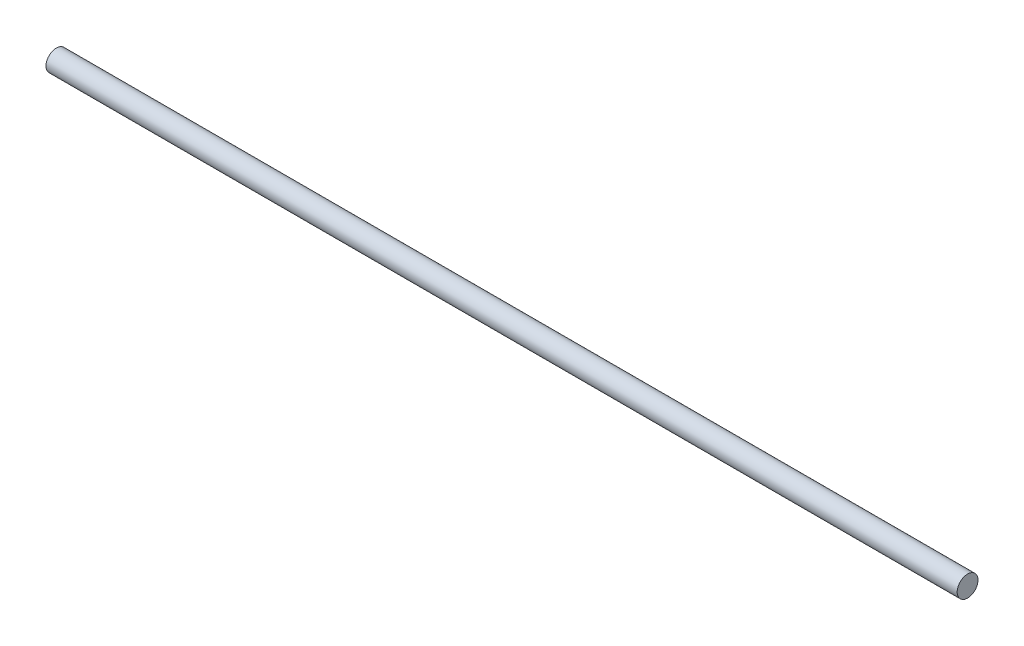
SolidWorks part; units mm, degrees
ref_plane "Front Plane" through (0, 0, 0) normal (0, 0, 1) x (1, 0, 0)
ref_plane "Top Plane" through (0, 0, 0) normal (0, 1, 0) x (1, 0, 0)
ref_plane "Right Plane" through (0, 0, 0) normal (1, 0, 0) x (0, 0, -1)
sketch "Sketch1" plane through (0, 0, 0) normal (1, 0, 0) x (0, 0, -1)
  circle A0 centre (0, 0) radius 4
  dimension "D1" = 8
extrude "Boss-Extrude1" add sketch "Sketch1" along normal blind 350
